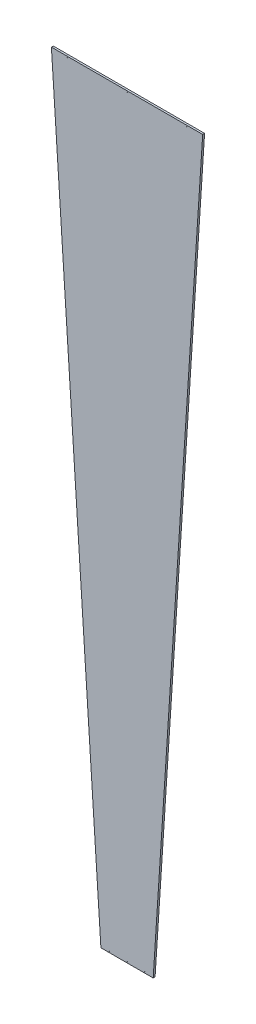
SolidWorks part; units mm, degrees
ref_plane "Plane1" through (0, 0, 0) normal (0, 0, 1) x (1, 0, 0)
ref_plane "Plane2" through (0, 0, 0) normal (0, 1, 0) x (1, 0, 0)
ref_plane "Plane3" through (0, 0, 0) normal (1, 0, 0) x (0, 0, -1)
ref_plane "Plane4" through (0, 0, 0) normal (0, 0, -1) x (-1, 0, 0)
sketch "Sketch1" plane through (0, 0, 0) normal (0, 0, -1) x (-1, 0, 0)
  line L0 (-4.387, 43.998) -> (4.387, 43.998)
  line L1 (0, 0) -> (11.1938, 170.7841) construction
  line L2 (12.697, 170.7841) -> (-12.697, 170.7841)
  line L3 (-11.1938, 170.7841) -> (0, 0) construction
  line L4 (12.6315, 169.7841) -> (-12.6315, 169.7841) construction
  line L5 (12.697, 170.7841) -> (4.387, 43.998)
  line L6 (0, 175.5878) -> (0, 0) construction
  line L7 (-12.697, 170.7841) -> (-4.387, 43.998)
  line L8 (4.4525, 44.998) -> (-4.4525, 44.998) construction
  dimension "D1" = 7.5
  dimension "D2" = 43.998
  dimension "D3" = 170.7841
  dimension "D4" = 1.5
  dimension "D5" = 126.7861
  dimension "D6" = 25.394
  dimension "D7" = 8.774
  dimension "D8" = 1
  dimension "D9" = 1
extrude "Extrude1" add sketch "Sketch1" against normal mid plane 0.32
ref_plane "Plane5" through (-2.8902, 44.0961, 0) normal (-0.0654, 0.9979, 0) x (-0.9979, -0.0654, 0)
ref_plane "Plane6" through (2.8902, 44.0961, 0) normal (-0.0654, -0.9979, 0) x (0.9979, -0.0654, 0)
sketch "Sketch2" plane through (0, 0, 0.16) normal (0, 0, 1) x (1, 0, 0)
  line L0 (0, 43.998) -> (0, 170.7841) construction
  line L1 (4.387, 43.998) -> (-4.387, 43.998) construction
  line L2 (-12.697, 170.7841) -> (12.697, 170.7841) construction
  circle A0 centre (-3, 44.198) radius 0.05
  circle A1 centre (0, 44.198) radius 0.05
  circle A2 centre (3, 44.198) radius 0.05
  circle A3 centre (0, 170.583) radius 0.05
  circle A4 centre (-10, 170.583) radius 0.05
  circle A5 centre (10, 170.583) radius 0.05
  dimension "D1" = 3
  dimension "D2" = 0.2
  dimension "D3" = 0.1
  dimension "D4" = 0.2011
  dimension "D5" = 10
  dimension "D6" = 126.585
extrude "Extrude2" cut sketch "Sketch2" against normal through all
sketch "Sketch3" plane through (0, 0, 0.16) normal (0, 0, 1) x (1, 0, 0)
  line L0 (-1.2501, 38.187) -> (-5.6627, 172.9788) construction
  line L1 (0, -55) -> (0, 55) construction
  line L2 (-3.6314, 44.9273) -> (0.6852, 45.0687) construction
  line L3 (4.387, 43.998) -> (-4.387, 43.998) construction
  line L4 (-2.7221, 44.9471) -> (-0.2234, 45.0289)
  line L5 (-2.7221, 44.9471) -> (-2.7227, 44.9671)
  line L6 (-0.2234, 45.0289) -> (-0.2241, 45.0489)
  line L7 (-2.7227, 44.9671) -> (-0.2241, 45.0489)
  point P5 (-1.4731, 44.998)
  dimension "D1" = 1.875
  dimension "D2" = 1
  dimension "D3" = 1.4731
  dimension "D4" = 0.02
  dimension "D5" = 2.5
extrude "Extrude3" [suppressed] cut sketch "Sketch3" against normal blind 0.02
pattern_linear "LPattern1" [suppressed] count 65 spacing 0.075
sketch "Sketch4" [suppressed] plane through (0, 0, 0.16) normal (0, 0, 1) x (1, 0, 0)
  line L0 (-2.8798, 49.7645) -> (-2.8791, 49.7445) construction
  line L2 (-2.8795, 49.7545) -> (-2.877, 49.6796) construction
  line L3 (-2.8773, 49.6896) -> (-2.8767, 49.6696) construction
  line L5 (-2.8782, 49.7171) -> (-4.7578, 49.6555) construction
  line L7 (-4.387, 43.998) -> (-12.697, 170.7841) construction
